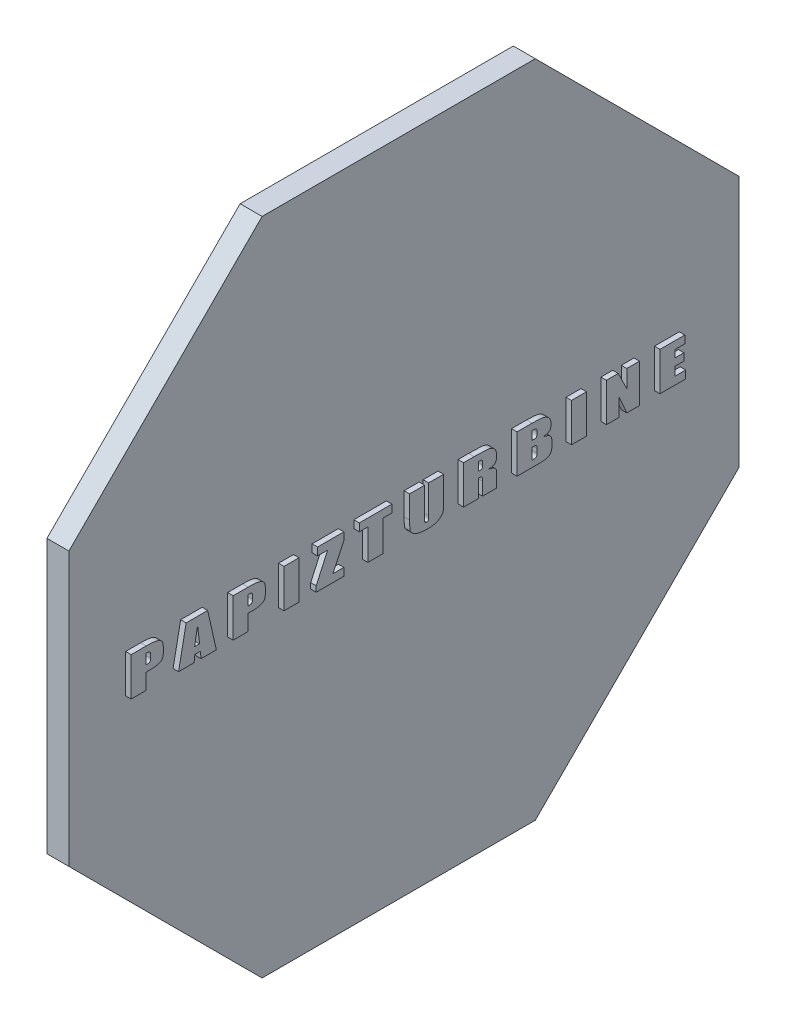
SolidWorks part; units mm, degrees
ref_plane "Front Plane" through (0, 0, 0) normal (0, 0, 1) x (1, 0, 0)
ref_plane "Top Plane" through (0, 0, 0) normal (0, 1, 0) x (1, 0, 0)
ref_plane "Right Plane" through (0, 0, 0) normal (1, 0, 0) x (0, 0, -1)
sketch "Sketch1" plane through (0, 0, 0) normal (1, 0, 0) x (0, 0, -1)
  line L0 (-42.4264, 36.2132) -> (0, -6.2132) construction
  line L1 (0, -6.2132) -> (42.4264, 36.2132) construction
  line L2 (-30, 6.2132) -> (-12.4264, 23.7868)
  line L3 (12.4264, 23.7868) -> (30.9634, 5.2498)
  line L4 (-30, -18.6396) -> (-12.4264, -36.2132)
  line L5 (12.4264, -36.2132) -> (30.9634, -17.6762)
  line L6 (-12.4264, 23.7868) -> (12.4264, 23.7868)
  line L7 (-30, 6.2132) -> (-30, -18.6396)
  line L8 (-12.4264, -36.2132) -> (12.4264, -36.2132)
  line L9 (30.9634, 5.2498) -> (30.9634, -17.6762)
  dimension "D1" = 30
  dimension "D2" = 30
  dimension "D3" = 30
extrude "Boss-Extrude1" add sketch "Sketch1" along normal blind 2
sketch "Sketch2" plane through (0, 0, 0) normal (-1, 0, 0) x (0, 0, 1)
  line L0 (0, 23.7868) -> (0, -36.2132) construction
  line L1 (-12.4264, 23.7868) -> (12.4264, 23.7868) construction
  line L2 (12.4264, -36.2132) -> (-12.4264, -36.2132) construction
  line L3 (-30.9634, -6.2132) -> (30, -6.2132) construction
  line L4 (-30.9634, -17.6762) -> (-30.9634, 5.2498) construction
  line L5 (30, 6.2132) -> (30, -18.6396) construction
  circle A0 centre (0, -6.2132) radius 28.115
  dimension "D1" = 56.23
extrude "Boss-Extrude2" add sketch "Sketch2" along normal blind 0.5
sketch "Sketch3" plane through (2, 0, 0) normal (1, 0, 0) x (0, 0, -1)
  line L0 (-30, -7.7814) -> (30.9634, -7.7814) construction
  text T0 "  PAPIZTURBINE" font "Impact" height 3.5
extrude "Boss-Extrude3" add sketch "Sketch3" along normal blind 0.5
